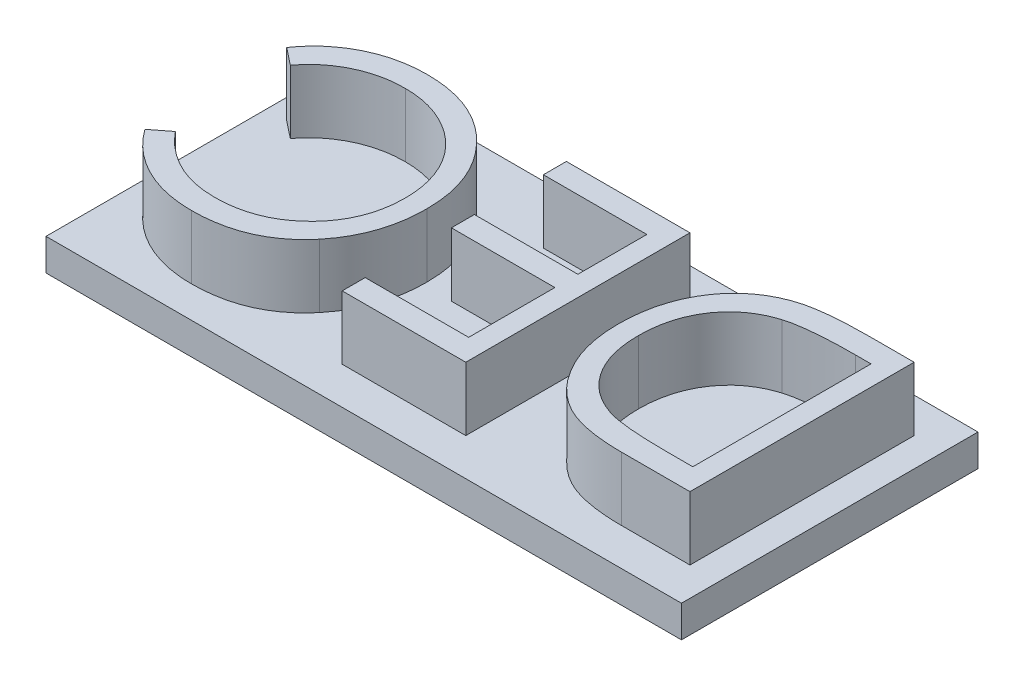
SolidWorks part; units mm, degrees
ref_plane "Front Plane" through (0, 0, 0) normal (0, 0, 1) x (1, 0, 0)
ref_plane "Top Plane" through (0, 0, 0) normal (0, 1, 0) x (1, 0, 0)
ref_plane "Right Plane" through (0, 0, 0) normal (1, 0, 0) x (0, 0, -1)
sketch "Sketch1" plane through (0, 0, 0) normal (0, 1, 0) x (1, 0, 0)
  line L1 (-7.5, 3.5) -> (7.5, 3.5)
  line L2 (-7.5, 3.5) -> (-7.5, -3.5)
  line L3 (-7.5, -3.5) -> (7.5, -3.5)
  line L4 (7.5, 3.5) -> (7.5, -3.5)
  line L5 (-7.5, 3.5) -> (7.5, -3.5) construction
  line L6 (-7.5, -3.5) -> (7.5, 3.5) construction
  point P0 (0, 0)
extrude "Boss-Extrude1" add sketch "Sketch1" along normal blind 0.75
sketch "Sketch2" plane through (0, 0.75, 0) normal (0, 1, 0) x (1, 0, 0)
  text T0 "DEC" font "Century Gothic" height in points 20
extrude "Boss-Extrude2" add sketch "Sketch2" along normal blind 1.5
